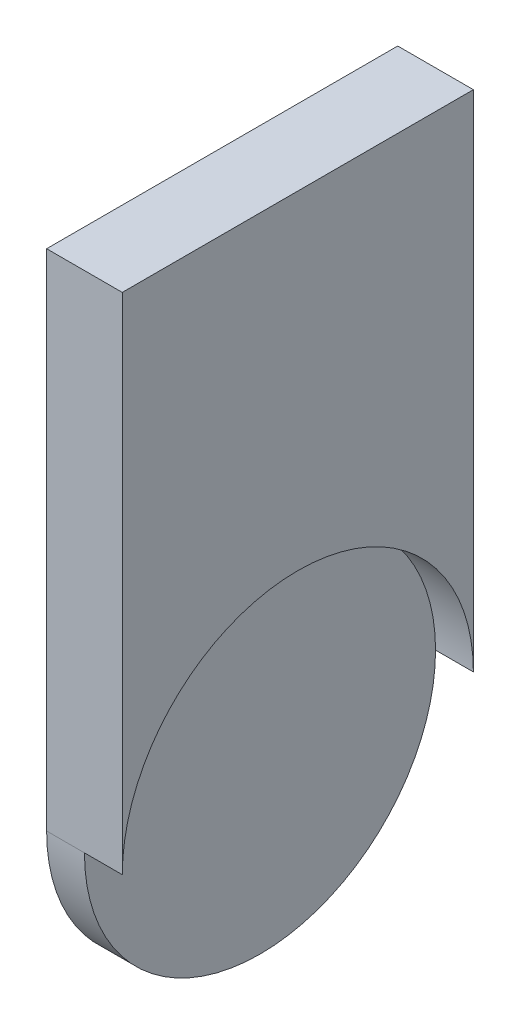
SolidWorks part; units mm, degrees
ref_plane "Plan de face" through (0, 0, 0) normal (0, 0, 1) x (1, 0, 0)
ref_plane "Plan de dessus" through (0, 0, 0) normal (0, 1, 0) x (1, 0, 0)
ref_plane "Plan de droite" through (0, 0, 0) normal (1, 0, 0) x (0, 0, -1)
sketch "Esquisse1" plane through (0, 0, 0) normal (1, 0, 0) x (0, 0, -1)
  line L1 (-15.3655, 38.894) -> (12.4845, 38.894)
  line L2 (-15.3655, 38.894) -> (-15.3655, -1.106)
  line L3 (-15.3655, -1.106) -> (12.4845, -1.106)
  line L4 (12.4845, 38.894) -> (12.4845, -1.106)
  arc A0 (12.4845, -1.106) -> (-15.3655, -1.106) centre (-1.4405, -1.106) cw
  dimension "D1" = 27.85
  dimension "D2" = 40
extrude "Boss.-Extru.1" add sketch "Esquisse1" along normal blind 6 contours L4 L1 L2 L3 | A0 L3
sketch "Esquisse2" plane through (6, 0, 0) normal (1, 0, 0) x (0, 0, -1)
  circle A0 centre (-1.4405, -1.106) radius 13.925
extrude "Enlèv. mat.-Extru.1" cut sketch "Esquisse2" against normal blind 3
